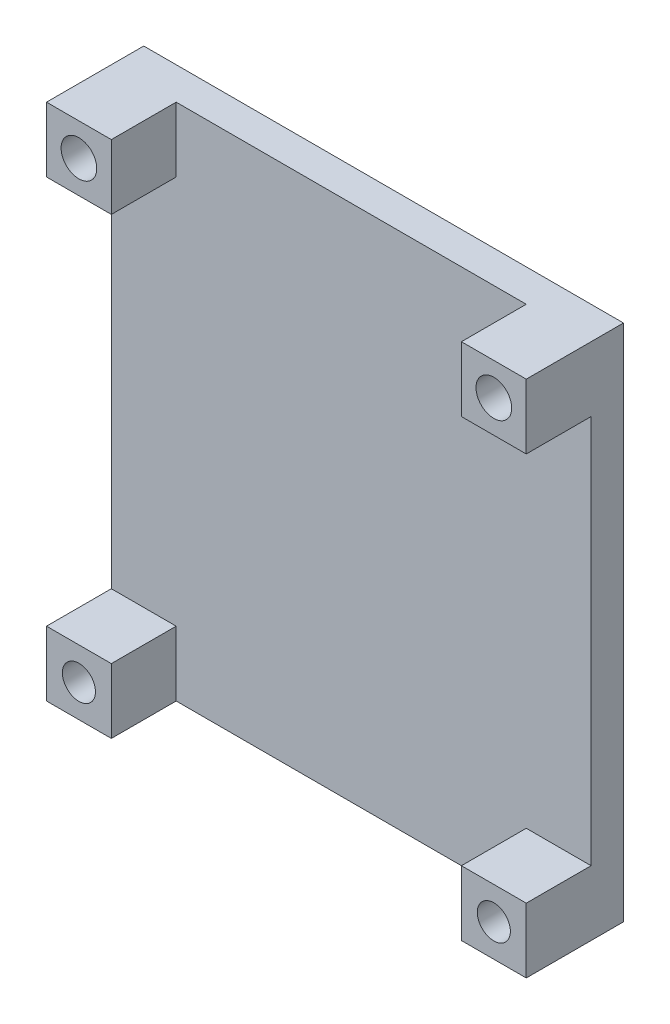
SolidWorks part; units mm, degrees
ref_plane "Alzado" through (0, 0, 0) normal (0, 0, 1) x (1, 0, 0)
ref_plane "Planta" through (0, 0, 0) normal (0, 1, 0) x (1, 0, 0)
ref_plane "Vista lateral" through (0, 0, 0) normal (1, 0, 0) x (0, 0, -1)
sketch "Croquis1" plane through (0, 0, 0) normal (0, 0, 1) x (1, 0, 0)
  line L0 (-66.3019, 41.2364) -> (7.6981, 41.2364)
  line L1 (7.6981, 41.2364) -> (7.6981, -38.7636)
  line L2 (7.6981, -38.7636) -> (-66.3019, -38.7636)
  line L3 (-66.3019, -38.7636) -> (-66.3019, 41.2364)
  dimension "D1" = 74
extrude "Saliente-Extruir1" add sketch "Croquis1" along normal blind 5
sketch "Croquis2" plane through (0, 0, 5) normal (0, 0, 1) x (1, 0, 0)
  line L0 (-66.3019, 41.2364) -> (-56.3019, 41.2364)
  line L1 (7.6981, 41.2364) -> (-66.3019, 41.2364) construction
  line L2 (-56.3019, 41.2364) -> (-56.3019, 31.2364)
  line L3 (-56.3019, 31.2364) -> (-66.3019, 31.2364)
  line L4 (-66.3019, 41.2364) -> (-66.3019, -38.7636) construction
  line L5 (-66.3019, 31.2364) -> (-66.3019, 41.2364)
  line L6 (-66.3019, -38.7636) -> (-66.3019, -28.7636)
  line L7 (-66.3019, -28.7636) -> (-56.3019, -28.7636)
  line L8 (-56.3019, -28.7636) -> (-56.3019, -38.7636)
  line L9 (-66.3019, -38.7636) -> (7.6981, -38.7636) construction
  line L10 (-56.3019, -38.7636) -> (-66.3019, -38.7636)
  line L11 (-66.3019, 41.2364) -> (-29.3019, 41.2364)
  line L12 (-29.3019, 41.2364) -> (-29.3019, 27.8769)
  line L13 (-2.3019, -38.7636) -> (7.6981, -38.7636)
  line L14 (-2.3019, -28.7636) -> (-2.3019, -38.7636)
  line L15 (7.6981, -28.7636) -> (-2.3019, -28.7636)
  line L16 (7.6981, -38.7636) -> (7.6981, -28.7636)
  line L17 (7.6981, 31.2364) -> (7.6981, 41.2364)
  line L18 (-2.3019, 31.2364) -> (7.6981, 31.2364)
  line L19 (-2.3019, 41.2364) -> (-2.3019, 31.2364)
  line L20 (7.6981, 41.2364) -> (-2.3019, 41.2364)
  circle A0 centre (-61.3019, 36.2364) radius 2.75
  circle A1 centre (-61.3019, -33.7636) radius 2.55
  circle A2 centre (2.6981, -33.7636) radius 2.55
  circle A3 centre (2.6981, 36.2364) radius 2.75
  line M1 (-66.3019, 41.2364) -> (-66.3019, -38.7636)
  line M2 (-66.3019, -38.7636) -> (7.6981, -38.7636)
  line M3 (7.6981, -38.7636) -> (7.6981, 41.2364)
  line M4 (7.6981, 41.2364) -> (-66.3019, 41.2364)
  dimension "D1" = 5.5
extrude "Saliente-Extruir2" add sketch "Croquis2" along normal blind 10 contours L3 L2 A0 M4 M1 | L19 L18 A3 M4 M3 | L15 L14 A2 M3 M2 | L8 L7 A1 M1 M2
